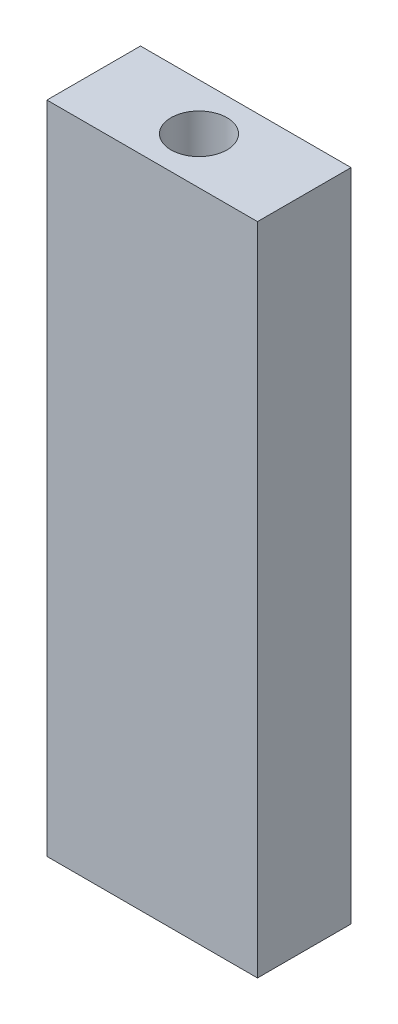
SolidWorks part; units mm, degrees
ref_plane "Front" through (0, 0, 0) normal (0, 0, 1) x (1, 0, 0)
ref_plane "Top" through (0, 0, 0) normal (0, 1, 0) x (1, 0, 0)
ref_plane "Right" through (0, 0, 0) normal (1, 0, 0) x (0, 0, -1)
sketch "Sketch1" plane through (0, 0, 0) normal (0, 1, 0) x (1, 0, 0)
  line L1 (-53.1168, 36.7917) -> (-38.8293, 36.7917)
  line L2 (-53.1168, 36.7917) -> (-53.1168, 30.4417)
  line L3 (-53.1168, 30.4417) -> (-38.8293, 30.4417)
  line L4 (-38.8293, 36.7917) -> (-38.8293, 30.4417)
  dimension "D1" = 14.2875
  dimension "D2" = 6.35
extrude "Extrude1" add sketch "Sketch1" along normal blind 44.45
hole_wizard "#6 Clearance Hole1" positions "Sketch3" profile "Sketch2" hole size "#6" standard "Ansi Inch"
sketch "Sketch3" plane through (0, 44.45, 0) normal (0, 1, 0) x (-1, 0, 0)
  line L0 (38.8293, -30.4417) -> (38.8293, -36.7917) construction
  line L1 (38.8293, -36.7917) -> (53.1168, -36.7917) construction
  point P0 (45.9731, -33.6167)
  point P7 (45.9731, -36.7917)
  dimension "D1" = 7.1437
  dimension "D2" = 3.175
sketch "Sketch2" plane through (-45.9731, 44.45, -33.6167) normal (1, 0, 0) x (0, 0, 1)
  line L0 (0, 0) -> (0, 7.4908)
  line L1 (0, 7.4908) -> (1.8986, 6.35)
  line L2 (1.8986, 6.35) -> (1.8986, 0)
  line L5 (1.8986, 0) -> (0, 0)
  line L10 (0, 7.4908) -> (-1.8986, 6.35) construction
  line L11 (0, -6.35) -> (0, 107.95) construction
  dimension "Hole Dia." = 3.7973
  dimension "Hole Depth" = 6.35
  dimension "Drill Angle" = 118
hole_wizard "#6 Clearance Hole2" positions "3DSketch1" profile "Sketch4" hole size "#6" standard "Ansi Inch"
sketch3d "3DSketch1"
  line L0 (-53.1168, 0, -30.4417) -> (-38.8293, 0, -30.4417) construction
  line L1 (-38.8293, 0, -30.4417) -> (-38.8293, 0, -36.7917) construction
  point P0 (-45.9731, 0, -33.6167)
  dimension "D1" = 3.175
  dimension "D2" = 7.1437
sketch "Sketch4" plane through (-45.9731, 0, -33.6167) normal (1, 0, 0) x (0, 0, -1)
  line L0 (0, 0) -> (0, 7.4908)
  line L1 (0, 7.4908) -> (1.8986, 6.35)
  line L2 (1.8986, 6.35) -> (1.8986, 0)
  line L5 (1.8986, 0) -> (0, 0)
  line L10 (0, 7.4908) -> (-1.8986, 6.35) construction
  line L11 (0, -6.35) -> (0, 107.95) construction
  dimension "Hole Dia." = 3.7973
  dimension "Hole Depth" = 6.35
  dimension "Drill Angle" = 118
